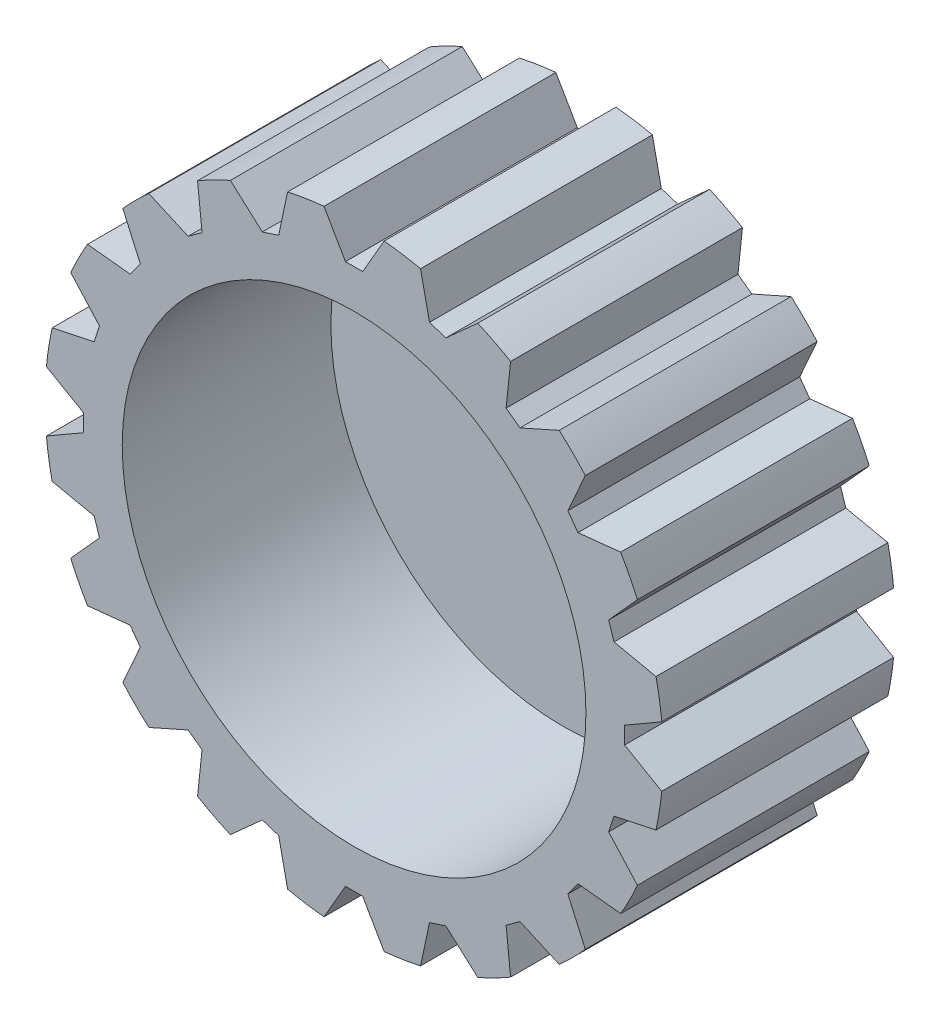
SolidWorks part; units mm, degrees
ref_plane "Front Plane" through (0, 0, 0) normal (0, 0, 1) x (1, 0, 0)
ref_plane "Top Plane" through (0, 0, 0) normal (0, 1, 0) x (1, 0, 0)
ref_plane "Right Plane" through (0, 0, 0) normal (1, 0, 0) x (0, 0, -1)
sketch "Sketch1" plane through (0, 0, 0) normal (0, 0, 1) x (1, 0, 0)
  circle A0 centre (0, 0) radius 40
  dimension "D1" = 80
extrude "Boss-Extrude1" add sketch "Sketch1" along normal blind 30
sketch "Sketch2" plane through (0, 0, 30) normal (0, 0, 1) x (1, 0, 0)
  line L0 (0, 40) -> (0, -40) construction
  line L1 (-138.9481, 40) -> (138.9481, 40) construction
  line L2 (4, 40) -> (-61.8149, -73.9948) construction
  line L3 (-4, 40) -> (61.8149, -73.9948) construction
  line L4 (-56.7722, 35) -> (68.1473, 35) construction
  line L5 (4, 40) -> (-4, 40)
  line L6 (-4, 40) -> (-1.1132, 35)
  line L7 (-1.1132, 35) -> (1.1132, 35)
  line L8 (1.1132, 35) -> (4, 40)
  line L9 (11.8744, 32.943) -> (16.1649, 36.8062)
  line L10 (16.1649, 36.8062) -> (8.5565, 39.2783)
  line L11 (8.5565, 39.2783) -> (9.7568, 33.631)
  line L12 (9.7568, 33.631) -> (11.8744, 32.943)
  line L13 (21.4731, 27.6612) -> (26.7475, 30.0095)
  line L14 (26.7475, 30.0095) -> (20.2753, 34.7118)
  line L15 (20.2753, 34.7118) -> (19.6718, 28.9699)
  line L16 (19.6718, 28.9699) -> (21.4731, 27.6612)
  line L17 (28.9699, 19.6718) -> (34.7118, 20.2753)
  line L18 (34.7118, 20.2753) -> (30.0095, 26.7475)
  line L19 (30.0095, 26.7475) -> (27.6612, 21.4731)
  line L20 (27.6612, 21.4731) -> (28.9699, 19.6718)
  line L21 (33.631, 9.7568) -> (39.2783, 8.5565)
  line L22 (39.2783, 8.5565) -> (36.8062, 16.1649)
  line L23 (36.8062, 16.1649) -> (32.943, 11.8744)
  line L24 (32.943, 11.8744) -> (33.631, 9.7568)
  line L25 (35, -1.1132) -> (40, -4)
  line L26 (40, -4) -> (40, 4)
  line L27 (40, 4) -> (35, 1.1132)
  line L28 (35, 1.1132) -> (35, -1.1132)
  line L29 (32.943, -11.8744) -> (36.8062, -16.1649)
  line L30 (36.8062, -16.1649) -> (39.2783, -8.5565)
  line L31 (39.2783, -8.5565) -> (33.631, -9.7568)
  line L32 (33.631, -9.7568) -> (32.943, -11.8744)
  line L33 (27.6612, -21.4731) -> (30.0095, -26.7475)
  line L34 (30.0095, -26.7475) -> (34.7118, -20.2753)
  line L35 (34.7118, -20.2753) -> (28.9699, -19.6718)
  line L36 (28.9699, -19.6718) -> (27.6612, -21.4731)
  line L37 (19.6718, -28.9699) -> (20.2753, -34.7118)
  line L38 (20.2753, -34.7118) -> (26.7475, -30.0095)
  line L39 (26.7475, -30.0095) -> (21.4731, -27.6612)
  line L40 (21.4731, -27.6612) -> (19.6718, -28.9699)
  line L41 (9.7568, -33.631) -> (8.5565, -39.2783)
  line L42 (8.5565, -39.2783) -> (16.1649, -36.8062)
  line L43 (16.1649, -36.8062) -> (11.8744, -32.943)
  line L44 (11.8744, -32.943) -> (9.7568, -33.631)
  line L45 (-1.1132, -35) -> (-4, -40)
  line L46 (-4, -40) -> (4, -40)
  line L47 (4, -40) -> (1.1132, -35)
  line L48 (1.1132, -35) -> (-1.1132, -35)
  line L49 (-11.8744, -32.943) -> (-16.1649, -36.8062)
  line L50 (-16.1649, -36.8062) -> (-8.5565, -39.2783)
  line L51 (-8.5565, -39.2783) -> (-9.7568, -33.631)
  line L52 (-9.7568, -33.631) -> (-11.8744, -32.943)
  line L53 (-21.4731, -27.6612) -> (-26.7475, -30.0095)
  line L54 (-26.7475, -30.0095) -> (-20.2753, -34.7118)
  line L55 (-20.2753, -34.7118) -> (-19.6718, -28.9699)
  line L56 (-19.6718, -28.9699) -> (-21.4731, -27.6612)
  line L57 (-28.9699, -19.6718) -> (-34.7118, -20.2753)
  line L58 (-34.7118, -20.2753) -> (-30.0095, -26.7475)
  line L59 (-30.0095, -26.7475) -> (-27.6612, -21.4731)
  line L60 (-27.6612, -21.4731) -> (-28.9699, -19.6718)
  line L61 (-33.631, -9.7568) -> (-39.2783, -8.5565)
  line L62 (-39.2783, -8.5565) -> (-36.8062, -16.1649)
  line L63 (-36.8062, -16.1649) -> (-32.943, -11.8744)
  line L64 (-32.943, -11.8744) -> (-33.631, -9.7568)
  line L65 (-35, 1.1132) -> (-40, 4)
  line L66 (-40, 4) -> (-40, -4)
  line L67 (-40, -4) -> (-35, -1.1132)
  line L68 (-35, -1.1132) -> (-35, 1.1132)
  line L69 (-32.943, 11.8744) -> (-36.8062, 16.1649)
  line L70 (-36.8062, 16.1649) -> (-39.2783, 8.5565)
  line L71 (-39.2783, 8.5565) -> (-33.631, 9.7568)
  line L72 (-33.631, 9.7568) -> (-32.943, 11.8744)
  line L73 (-27.6612, 21.4731) -> (-30.0095, 26.7475)
  line L74 (-30.0095, 26.7475) -> (-34.7118, 20.2753)
  line L75 (-34.7118, 20.2753) -> (-28.9699, 19.6718)
  line L76 (-28.9699, 19.6718) -> (-27.6612, 21.4731)
  line L77 (-19.6718, 28.9699) -> (-20.2753, 34.7118)
  line L78 (-20.2753, 34.7118) -> (-26.7475, 30.0095)
  line L79 (-26.7475, 30.0095) -> (-21.4731, 27.6612)
  line L80 (-21.4731, 27.6612) -> (-19.6718, 28.9699)
  line L81 (-9.7568, 33.631) -> (-8.5565, 39.2783)
  line L82 (-8.5565, 39.2783) -> (-16.1649, 36.8062)
  line L83 (-16.1649, 36.8062) -> (-11.8744, 32.943)
  line L84 (-11.8744, 32.943) -> (-9.7568, 33.631)
  circle A0 centre (0, 0) radius 40 construction
  point P14 (0, 0)
  point P94 (0, 0)
  dimension "D1" = 60
  dimension "D2" = 4
  dimension "D3" = 5
extrude "Cut-Extrude1" cut sketch "Sketch2" against normal up to vertex (30 mm away) up to point (0, 0, 0)
sketch "Sketch3" plane through (0, 0, 30) normal (0, 0, 1) x (1, 0, 0)
  circle A0 centre (0, 0) radius 30
  dimension "D1" = 60
extrude "Cut-Extrude2" cut sketch "Sketch3" against normal blind 27
sketch "Sketch4" plane through (0, 0, 3) normal (0, 0, 1) x (1, 0, 0)
  line L0 (0, 0) -> (0, 74.1987) construction
  line L1 (0, 0) -> (95.805, 0) construction
  line L2 (0, 0) -> (-75.0259, 0) construction
  line L3 (0, 0) -> (0, -62.4859) construction
  line L4 (0, 0) -> (38.1173, 38.1173) construction
  circle A0 centre (8.5, 0) radius 1.5
  circle A1 centre (-8.5, 0) radius 1.5
  circle A2 centre (0, -8.5) radius 1.5
  circle A3 centre (0, 8.5) radius 1.5
  circle A4 centre (0, 0) radius 3.5
  dimension "D2" = 8.5
  dimension "D3" = 7
  dimension "D1" = 90
extrude "Cut-Extrude3" cut sketch "Sketch4" against normal blind 27
